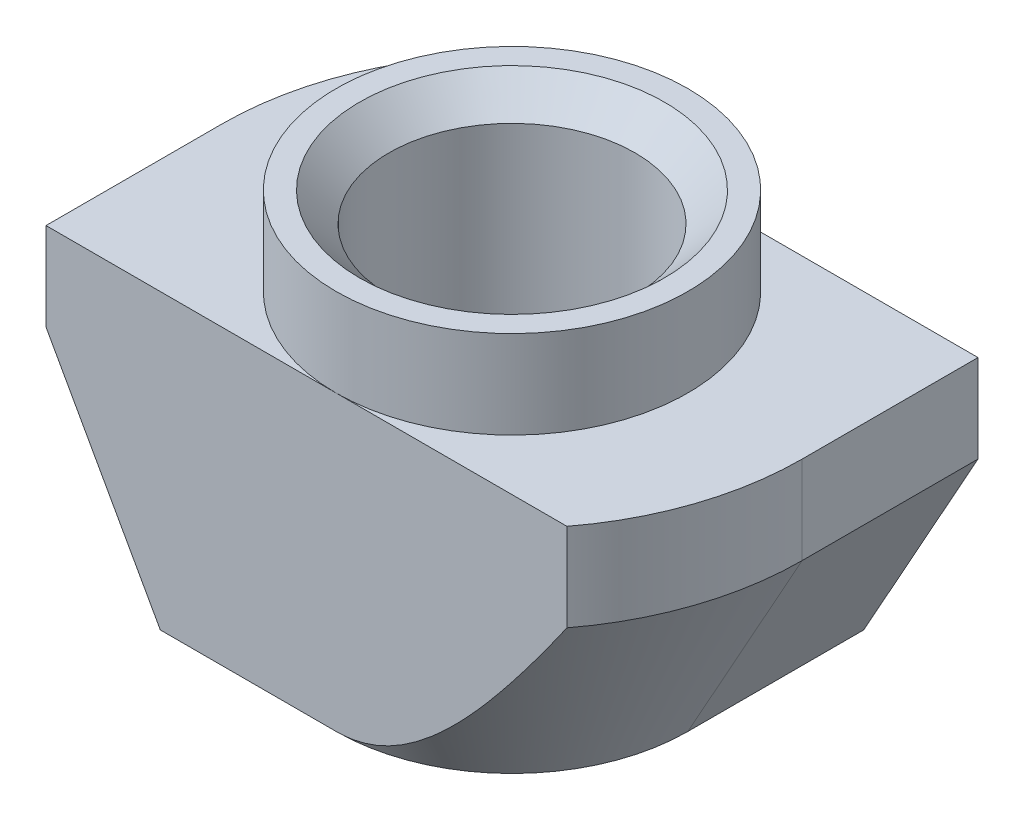
SolidWorks part; units mm, degrees
material "Сталь 20  ГОСТ 1050-2013"
ref_plane "Спереди" through (0, 0, 0) normal (0, 0, 1) x (1, 0, 0)
ref_plane "Сверху" through (0, 0, 0) normal (0, 1, 0) x (1, 0, 0)
ref_plane "Справа" through (0, 0, 0) normal (1, 0, 0) x (0, 0, -1)
sketch "Эскиз1" plane through (0, 0, 0) normal (0, 0, 1) x (1, 0, 0)
  line L0 (3, 0) -> (-3, 0)
  line L1 (-3, 0) -> (-3, -1.5)
  line L2 (-3, -1.5) -> (-4.95, -1.5)
  line L3 (-4.95, -1.5) -> (-4.95, -6.5)
  line L4 (-4.95, -6.5) -> (4.95, -6.5)
  line L5 (0, -6.5) -> (0, 0) construction
  line L6 (4.95, -1.5) -> (4.95, -6.5)
  line L7 (3, -1.5) -> (4.95, -1.5)
  line L8 (3, 0) -> (3, -1.5)
  dimension "D1" = 6
  dimension "D2" = 9.9
  dimension "D3" = 6.5
  dimension "D4" = 1.5
extrude "Бобышка-Вытянуть1" add sketch "Эскиз1" along normal mid plane 6
hole_wizard "Отверстие обработанное метчиком M51" positions "Эскиз2" profile "Эскиз3" tap size "M5" standard "ISO" end condition up to next
sketch "Эскиз2" plane through (0, 0, 0) normal (0, 1, 0) x (1, 0, 0)
  point P0 (0, 0)
sketch "Эскиз3" plane through (0, 0, 0) normal (1, 0, 0) x (0, 0, 1)
  line L0 (0, 0) -> (0, 6.5)
  line L1 (0, 6.5) -> (2.6, 6.5)
  line L2 (2.1, 6) -> (2.1, 0.5)
  line L3 (2.1, 0.5) -> (2.6, 0)
  line L5 (2.6, 0) -> (0, 0)
  line L6 (-2.1, 0.5) -> (-2.6, 0) construction
  line L7 (2.6, 6.5) -> (2.1, 6)
  line L8 (-2.6, 6.5) -> (-2.1, 6) construction
  line L11 (0, -6.35) -> (0, 107.95) construction
  dimension "Диаметр проходного сверла" = 4.2
  dimension "Глубина проходного сверла" = 6.5
  dimension "Диаметр передней зенковки" = 5.2
  dimension "Угол передней зенковки" = 90
  dimension "Диаметр задней зенковки" = 5.2
  dimension "Угол задней зенковки" = 90
cosmetic thread "Отверстие резьбы1" parameters "D2"=5
sketch "Эскиз4" plane through (0, 0, 0) normal (0, 1, 0) x (1, 0, 0)
  line L8 (-3, -3) -> (-3, 3) construction
  circle A2 centre (0, 0) radius 3
extrude "Вырез-Вытянуть1" cut sketch "Эскиз4" against normal up to surface (1.5 mm away) flip side to cut up to face at (-3.975, -1.5, 0)
sketch "Эскиз5" plane through (0, -1.5, 0) normal (0, 1, 0) x (1, 0, 0)
  line L0 (-4.95, 0) -> (-4.95, 3)
  line L1 (-4.95, -3) -> (-4.95, 3) construction
  line L2 (-4.95, 3) -> (-3.9373, 3)
  line L3 (0, 3) -> (-4.95, 3) construction
  line L4 (4.95, 0) -> (4.95, -3)
  line L5 (4.95, -3) -> (4.95, 3) construction
  line L6 (4.95, -3) -> (3.9373, -3)
  line L7 (4.95, -3) -> (0, -3) construction
  arc A0 (-3.9373, 3) -> (-4.95, 0) centre (0, 0) ccw
  arc A2 (4.95, 0) -> (3.9373, -3) centre (0, 0) cw
extrude "Вырез-Вытянуть2" cut sketch "Эскиз5" against normal through all
sketch "Эскиз6" plane through (0, 0, 3) normal (0, 0, 1) x (1, 0, 0)
  line L0 (-4.95, -3) -> (-4.95, -6.5)
  line L1 (-4.95, -1.5) -> (-4.95, -6.5) construction
  line L2 (-4.95, -6.5) -> (-3, -6.5)
  line L3 (-4.95, -6.5) -> (3.9373, -6.5) construction
  line L4 (-3, -6.5) -> (-4.95, -3)
  line L5 (0, -1.5) -> (-4.95, -1.5) construction
  line L7 (-3, 0) -> (-3, -1.5) construction
  point P10 (0, 0)
  dimension "D1" = 1.5
sketch "Эскиз7" plane through (0, -6.5, 0) normal (0, -1, 0) x (1, 0, 0)
  line L0 (0, 4.95) -> (-4.95, 4.95)
  line L1 (-4.95, 4.95) -> (-4.95, 0)
  line L2 (0, -4.95) -> (4.95, -4.95)
  line L3 (4.95, -4.95) -> (4.95, 0)
  arc A0 (-4.95, 0) -> (0, -4.95) centre (0, 0) ccw
  arc A1 (4.95, 0) -> (0, 4.95) centre (0, 0) ccw
sweep "Вырез-По траектории1" cut profiles "Эскиз6" path "Эскиз7"
